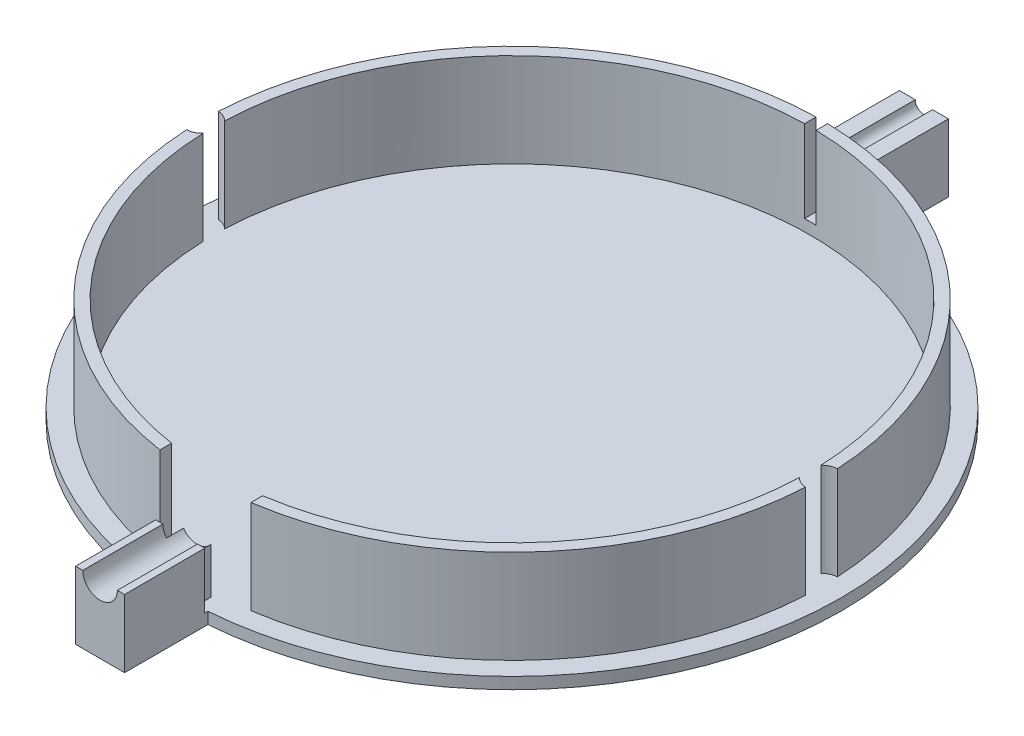
SolidWorks part; units mm, degrees
ref_plane "Front Plane" through (0, 0, 0) normal (0, 0, 1) x (1, 0, 0)
ref_plane "Top Plane" through (0, 0, 0) normal (0, 1, 0) x (1, 0, 0)
ref_plane "Right Plane" through (0, 0, 0) normal (1, 0, 0) x (0, 0, -1)
sketch "Sketch1" plane through (0, 0, 0) normal (0, 1, 0) x (1, 0, 0)
  circle A0 centre (0, 0) radius 57.15
  dimension "D1" = 114.3
extrude "Boss-Extrude1" add sketch "Sketch1" along normal blind 2
sketch "Sketch2" plane through (0, 2, 0) normal (0, 1, 0) x (1, 0, 0)
  circle A0 centre (0, 0) radius 53.75
  circle A1 centre (0, 0) radius 51.75
  circle A2 centre (0, 0) radius 57.15 construction
  dimension "D1" = 2
  dimension "D2" = 3.4
extrude "Boss-Extrude2" add sketch "Sketch2" along normal blind 16.25
sketch "Sketch4" plane through (0, 18.25, 0) normal (0, 1, 0) x (1, 0, 0)
  arc A0 (51.7169, -1.8517) -> (53.6797, -2.7491) centre (53.75, 0) ccw
  circle A1 centre (0, 0) radius 53.75 construction
  arc A2 (-53.6797, -2.7491) -> (-51.7169, -1.8517) centre (-53.75, 0) ccw
  circle A3 centre (0, 0) radius 51.75 construction
  arc A4 (-51.7169, 1.8517) -> (-51.7169, -1.8517) centre (0, 0) ccw
  arc A5 (-53.6797, 2.7491) -> (-53.6797, -2.7491) centre (0, 0) ccw
  arc A6 (51.7169, -1.8517) -> (51.7169, 1.8517) centre (0, 0) ccw
  arc A7 (53.6797, -2.7491) -> (53.6797, 2.7491) centre (0, 0) ccw
  arc A8 (-51.7169, 1.8517) -> (-53.6797, 2.7491) centre (-53.75, 0) ccw
  arc A9 (53.6797, 2.7491) -> (51.7169, 1.8517) centre (53.75, 0) ccw
  circle M1 centre (0, 0) radius 53.75
  circle M2 centre (0, 0) radius 51.75
  dimension "D1" = 5.5
  dimension "D2" = 5.5
extrude "Cut-Extrude1" cut sketch "Sketch4" against normal up to surface (16.25 mm away) contours A9 A0 M1 M2 | A4 A2 A5 A8 up to face at (0, 2, 57.15)
sketch "Sketch5" plane through (0, 18.25, 0) normal (0, 1, 0) x (1, 0, 0)
  line L0 (0, -51.75) -> (0, -53.75)
  line L1 (3, -51.663) -> (3, -53.6662)
  line L2 (-3, -51.663) -> (-3, -53.6662)
  line L3 (3, -51.75) -> (3, -53.75) construction
  line L4 (-3, -51.75) -> (-3, -53.75) construction
  arc A0 (-51.7169, -1.8517) -> (51.7169, -1.8517) centre (0, 0) ccw construction
  arc A1 (-53.6797, -2.7491) -> (53.6797, -2.7491) centre (0, 0) ccw construction
  arc A3 (-3, -51.663) -> (3, -51.663) centre (0, 0) ccw
  arc A4 (-3, -53.6662) -> (3, -53.6662) centre (0, 0) ccw
  arc M2 (-53.6797, -2.7491) -> (53.6797, -2.7491) centre (0, 0) ccw
  arc M4 (51.7169, -1.8517) -> (-51.7169, -1.8517) centre (0, 0) cw
  dimension "D1" = 3
  dimension "D2" = 3
extrude "Cut-Extrude2" cut sketch "Sketch5" against normal blind 6.8 contours L2 L0 M4 M2 | L1 L0 M4 M2
sketch "Sketch7" plane through (0, 2, 0) normal (0, 1, 0) x (1, 0, 0)
  line L2 (2.4, -54.5711) -> (2.4, -57.0996)
  line L3 (-2.4, -54.5711) -> (-2.4, -57.0996)
  line L4 (3, -51.663) -> (3, -53.6662) construction
  circle A0 centre (0, 0) radius 57.15 construction
  arc A1 (-2.4, -57.0996) -> (2.4, -57.0996) centre (0, 0) ccw
  arc A2 (-2.4, -54.5711) -> (2.4, -54.5711) centre (0, 0) ccw
  dimension "D1" = 4.8
  dimension "D2" = 0.6
extrude "Boss-Extrude5" add sketch "Sketch7" along normal up to surface (16.25 mm away) up to face at (-32.6748, 18.25, 32.3169)
ref_plane "Plane1" through (0, 0, 57.15) normal (0, 0, 1) x (1, 0, 0)
sketch "Sketch8" plane through (0, 0, 57.15) normal (0, 0, 1) x (1, 0, 0)
  line L0 (2.4, 18.25) -> (-2.4, 18.25) construction
  line L1 (2.4, 18.25) -> (-2.4, 18.25)
  line L2 (57.15, 2) -> (-57.15, 2) construction
  line L3 (2.4, 2) -> (-2.4, 2)
  line L4 (2.4, 18.25) -> (2.4, 2) construction
  line L5 (2.4, 18.25) -> (2.4, 2)
  line L6 (-2.4, 18.25) -> (-2.4, 2) construction
  line L7 (-2.4, 18.25) -> (-2.4, 2)
  line L8 (-2.4, 11.75) -> (2.4, 11.75)
  circle A0 centre (0, 11.75) radius 3
  dimension "D2" = 6
  dimension "D1" = 9.75
extrude "Cut-Extrude3" cut sketch "Sketch8" against normal blind 7.6 contours L7 A0 L5 L8 | L5 A0 L7 L8 | A0 L5 L1 L7 | L5 A0 | L7 A0
sketch "Sketch9" plane through (0, 0, 0) normal (0, 0, 1) x (1, 0, 0)
  line L0 (51.7169, 18.25) -> (-51.7169, 18.25) construction
  line L1 (-1, 4) -> (1, 4)
  line L2 (-1, 4) -> (-1, 18.25)
  line L3 (-1, 6) -> (1, 6)
  line L4 (1, 4) -> (1, 18.25)
  line L5 (-1, 4) -> (1, 6) construction
  line L6 (-1, 6) -> (1, 4) construction
  line L7 (1, 18.25) -> (-1, 18.25)
  point P0 (0, 5)
  dimension "D1" = 5
  dimension "D2" = 2
  dimension "D3" = 2
extrude "Cut-Extrude4" cut sketch "Sketch9" against normal through all contours L1 L4 L3 L2 | L4 L7 L2 L3
sketch "Sketch11" plane through (0, 18.25, 0) normal (0, 1, 0) x (1, 0, 0)
  line L2 (-7.9, -27.9874) -> (7.9, -27.9874)
  line L4 (7.9, -49.3687) -> (-7.9, -49.3687)
  line L5 (7.9, -49.3687) -> (7.9, -53.9572)
  line L6 (7.9, -53.9572) -> (-7.9, -53.9572)
  line L7 (-7.9, -49.3687) -> (-7.9, -53.9572)
  line L8 (7.9, -49.3687) -> (-7.9, -53.9572) construction
  line L9 (7.9, -53.9572) -> (-7.9, -49.3687) construction
  arc A2 (3, -51.663) -> (51.7169, -1.8517) centre (0, 0) ccw construction
  arc A3 (3, -51.663) -> (51.7169, -1.8517) centre (0, 0) ccw
  point P7 (0, -51.663)
  dimension "D1" = 15.8
extrude "Cut-Extrude5" cut sketch "Sketch11" against normal up to surface (16.25 mm away)
sketch "Sketch12" plane through (0, 0, 0) normal (0, -1, 0) x (1, 0, 0)
  line L0 (0, 57.15) -> (0, 71.44)
  line L1 (-4.25, 57.15) -> (4.25, 57.15)
  line L2 (4.25, 56.9918) -> (4.25, 71.44)
  line L3 (-4.25, 56.9918) -> (-4.25, 71.44)
  line L4 (-4.25, 71.44) -> (4.25, 71.44)
  line L5 (5.5481, 0) -> (-4.25, 0)
  line L6 (-14.4841, 71.44) -> (8.5, 71.44) construction
  line L7 (-14.4841, 57.15) -> (8.5, 57.15) construction
  line L8 (-4.25, -71.44) -> (4.25, -71.44)
  line L9 (-4.25, -56.9918) -> (-4.25, -71.44)
  line L10 (4.25, -56.9918) -> (4.25, -71.44)
  line L11 (-4.25, -57.15) -> (4.25, -57.15)
  line L12 (0, -57.15) -> (0, -71.44)
  circle A0 centre (0, 0) radius 57.15 construction
  circle A1 centre (0, 0) radius 57.15
  point P6 (4.25, 0)
  point P8 (-4.25, 0)
  circle M1 centre (0, 0) radius 57.15
  dimension "D1" = 14.29
  dimension "D5" = 14.29
extrude "Boss-Extrude7" add sketch "Sketch12" against normal blind 2 contours L4 L0 L1 L2 | L4 L3 L1 L0 | L2 L1 M1 | L3 L1 M1 | L11 L12 L8 L10 | L12 L11 L9 L8 | L9 L11 M1 | L11 L10 M1 | A1
sketch "Sketch13" plane through (0, 0, 71.44) normal (0, 0, 1) x (1, 0, 0)
  line L0 (-4.25, 2) -> (4.25, 2) construction
  line L1 (-4.25, 2) -> (4.25, 2)
  line L2 (-3, 11.75) -> (-4.25, 11.75)
  line L3 (4.25, 2) -> (-4.25, 2)
  line L4 (4.25, 2) -> (4.25, 11.75)
  line L5 (4.25, 11.75) -> (3, 11.75)
  line L6 (-4.25, 2) -> (-4.25, 11.75)
  arc A0 (-3, 11.75) -> (3, 11.75) centre (0, 11.75) ccw
  dimension "D2" = 6
  dimension "D1" = 9.75
extrude "Boss-Extrude8" add sketch "Sketch13" against normal blind 13.9 contours L3 L6 L2 A0 L5 L4
sketch "Sketch14" plane through (0, 0, 57.15) normal (0, 0, 1) x (1, 0, 0)
  line L3 (-2.4, 2) -> (2.4, 2)
  line L4 (2.4, 2) -> (2.4, 9.95)
  line L5 (-2.4, 9.95) -> (-2.4, 2)
  line L6 (-2.4, 2) -> (2.4, 2)
  line L7 (2.4, 2) -> (2.4, 9.95)
  line L8 (-2.4, 9.95) -> (-2.4, 2)
  arc A1 (-2.4, 9.95) -> (2.4, 9.95) centre (0, 11.75) ccw
  arc A2 (-2.4, 9.95) -> (2.4, 9.95) centre (0, 11.75) ccw
  dimension "D1" = 0
extrude "Boss-Extrude9" add sketch "Sketch14" along normal blind 2 and the other way blind 2
sketch "Sketch15" plane through (0, 0, -71.44) normal (0, 0, -1) x (-1, 0, 0)
  line L0 (-1.5, 11.75) -> (-4.25, 11.75)
  line L1 (4.25, 0) -> (-4.25, 0)
  line L2 (4.25, 0) -> (4.25, 11.75)
  line L3 (4.25, 11.75) -> (1.5, 11.75)
  line L4 (-4.25, 0) -> (-4.25, 11.75)
  arc A0 (-1.5, 11.75) -> (1.5, 11.75) centre (0, 11.75) ccw
  dimension "D2" = 3
  dimension "D1" = 11.75
extrude "Boss-Extrude10" add sketch "Sketch15" against normal blind 13.9
